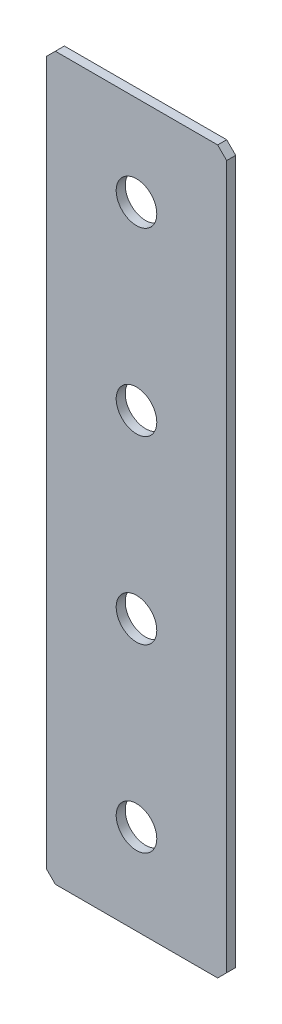
SolidWorks part; units mm, degrees
material "Простая углеродистая сталь"
ref_plane "Спереди(Плоскость XY)" through (0, 0, 0) normal (0, 0, 1) x (1, 0, 0)
ref_plane "Сверху(Плоскость XZ)" through (0, 0, 0) normal (0, 1, 0) x (1, 0, 0)
ref_plane "Справа(Плоскость ZY)" through (0, 0, 0) normal (1, 0, 0) x (0, 0, -1)
sketch "Эскиз1" plane through (0, 0, 0) normal (0, 0, 1) x (1, 0, 0)
  line L1 (-20, -80) -> (20, -80)
  line L2 (-20, -80) -> (-20, 80)
  line L3 (-20, 80) -> (20, 80)
  line L4 (20, -80) -> (20, 80)
  line L5 (-20, -80) -> (20, 80) construction
  line L6 (-20, 80) -> (20, -80) construction
  point P0 (0, 0)
  dimension "D1" = 40
  dimension "D2" = 160
extrude "Бобышка-Вытянуть1" add sketch "Эскиз1" along normal blind 2
chamfer "Фаска1" distance 2 angle 45 4 edges at (-20, -80, 1) (20, -80, 1) (-20, 80, 1) (20, 80, 1)
hole_wizard "Отверстие с зазором M81" positions "Эскиз2" profile "Эскиз3" hole size "M8" standard "DIN" end condition through all
sketch "Эскиз2" plane through (0, 0, 2) normal (0, 0, 1) x (1, 0, 0)
  line L12 (0, 80) -> (0, -80) construction
  line L13 (18, 80) -> (-18, 80) construction
  line L14 (-18, -80) -> (18, -80) construction
  point P204 (0, 60)
  point P206 (0, 20)
  point P208 (0, -20)
  point P210 (0, -60)
  dimension "D1" = 40
  dimension "D2" = 40
  dimension "D3" = 40
  dimension "D4" = 20
sketch "Эскиз3" plane through (0, -60, 2) normal (1, 0, 0) x (0, -1, 0)
  line L0 (0, 0) -> (0, 2)
  line L1 (0, 2) -> (4.5, 2)
  line L2 (4.5, 2) -> (4.5, 0)
  line L5 (4.5, 0) -> (0, 0)
  line L11 (0, -6.35) -> (0, 107.95) construction
  dimension "Диаметр сквозного отверстия" = 9
  dimension "Глубина сквозного отверстия" = 2
